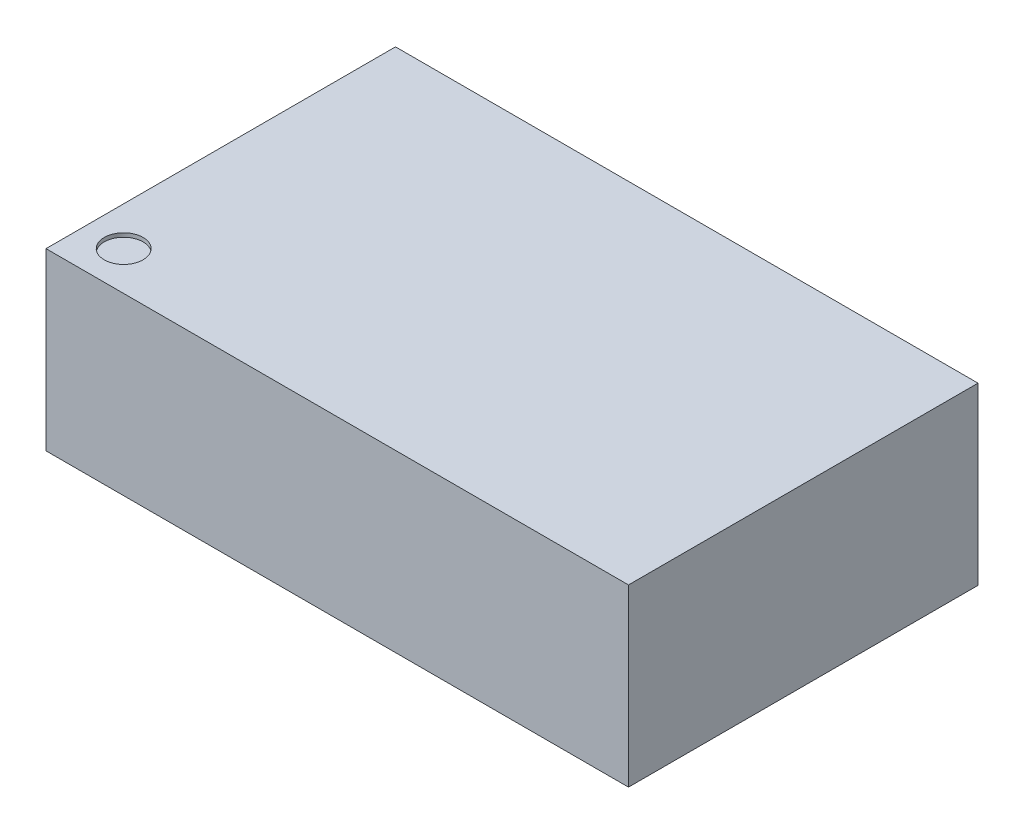
SolidWorks part; units mm, degrees
ref_plane "Front Plane" through (0, 0, 0) normal (0, 0, 1) x (1, 0, 0)
ref_plane "Top Plane" through (0, 0, 0) normal (0, 1, 0) x (1, 0, 0)
ref_plane "Right Plane" through (0, 0, 0) normal (1, 0, 0) x (0, 0, -1)
sketch "Sketch1" plane through (0, 0, 0) normal (0, 1, 0) x (1, 0, 0)
  line L1 (-7.5, -4.5) -> (7.5, -4.5)
  line L2 (-7.5, -4.5) -> (-7.5, 4.5)
  line L3 (-7.5, 4.5) -> (7.5, 4.5)
  line L4 (7.5, -4.5) -> (7.5, 4.5)
  line L5 (-7.5, -4.5) -> (7.5, 4.5) construction
  line L6 (-7.5, 4.5) -> (7.5, -4.5) construction
  point P0 (0, 0)
  dimension "D1" = 15
  dimension "D2" = 9
extrude "Boss-Extrude1" add sketch "Sketch1" along normal blind 4.51
sketch "Sketch2" plane through (0, 4.51, 0) normal (0, 1, 0) x (1, 0, 0)
  line L0 (-7.5, 4.5) -> (-7.5, -4.5) construction
  line L1 (-7.5, -4.5) -> (7.5, -4.5) construction
  circle A0 centre (-6.5, -3.5) radius 0.5
  dimension "D1" = 1
  dimension "D2" = 1
  dimension "D3" = 1
extrude "Cut-Extrude1" cut sketch "Sketch2" against normal blind 0.1
